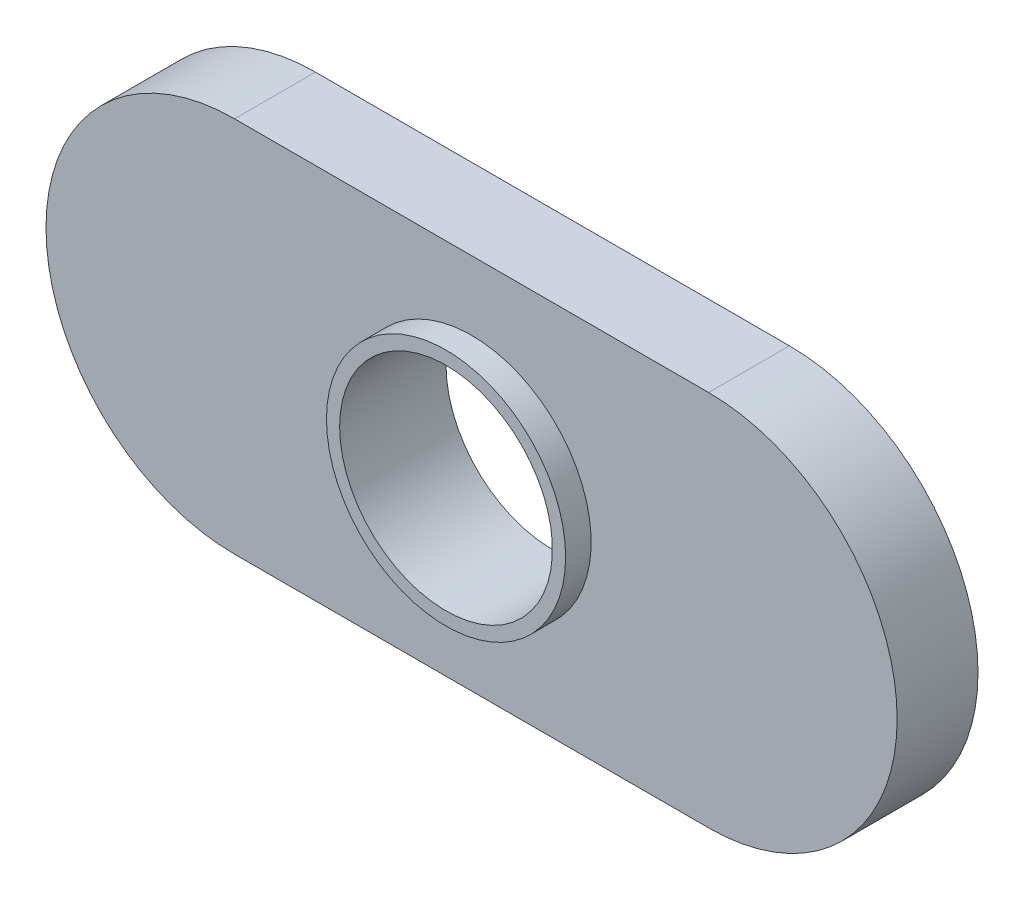
SolidWorks part; units mm, degrees
material "AISI 1020"
ref_plane "Front Plane" through (0, 0, 0) normal (0, 0, 1) x (1, 0, 0)
ref_plane "Top Plane" through (0, 0, 0) normal (0, 1, 0) x (1, 0, 0)
ref_plane "Right Plane" through (0, 0, 0) normal (1, 0, 0) x (0, 0, -1)
sketch "Sketch1" plane through (0, 0, 0) normal (0, 0, 1) x (1, 0, 0)
  line L0 (105.6526, 125.9331) -> (131.0526, 125.9331) construction
  line L88 (111.2787, 131.5592) -> (125.4265, 131.5592)
  line L89 (111.2787, 120.307) -> (125.4265, 120.307)
  arc A0 (111.2787, 120.307) -> (111.2787, 131.5592) centre (111.2787, 125.9331) cw
  arc A1 (125.4265, 120.307) -> (125.4265, 131.5592) centre (125.4265, 125.9331) ccw
  point P4 (105.6526, 125.9331)
  dimension "D1" = 11.2522
  dimension "D2" = 25.4
extrude "Extrude1" add sketch "Sketch1" along normal blind 2.413
sketch "Sketch4" plane through (0, 0, 2.413) normal (0, 0, 1) x (1, 0, 0)
  line L0 (111.2185, 131.5588) -> (125.4866, 131.5588) construction
  line L1 (105.6526, 125.9331) -> (131.0526, 125.9331) construction
  circle A0 centre (118.3526, 125.9331) radius 3.5687
  arc A1 (111.2787, 131.5592) -> (111.2787, 120.307) centre (111.2787, 125.9331) ccw construction
  arc A2 (125.4265, 120.307) -> (125.4265, 131.5592) centre (125.4265, 125.9331) ccw construction
  dimension "D1" = 7.1374
  dimension "D2" = 7.134
extrude "Extrude3" add sketch "Sketch4" along normal blind 0.762
sketch "Sketch6" plane through (0, 0, 0) normal (0, 0, -1) x (-1, 0, 0)
  circle A0 centre (-118.3526, 125.9331) radius 3.175
  dimension "D1" = 6.35
extrude "Cut-Extrude1" cut sketch "Sketch6" against normal through all
